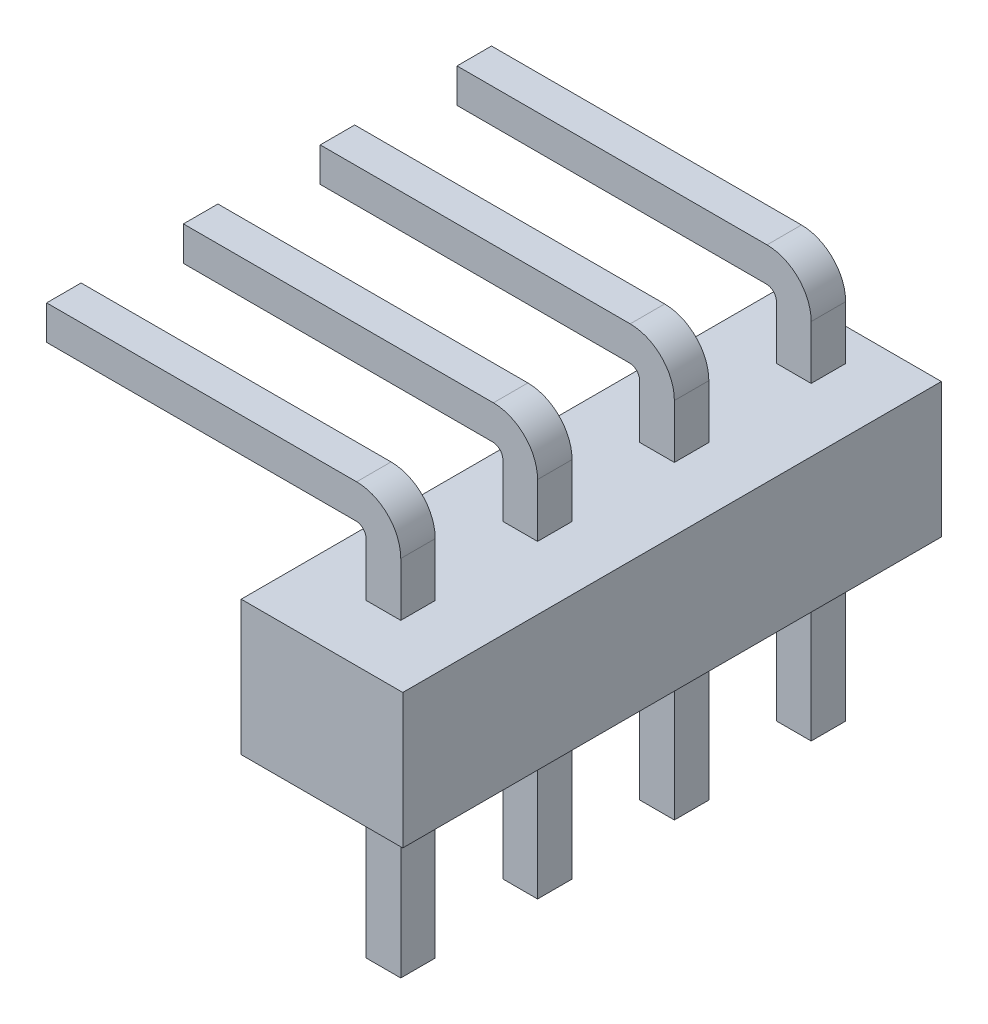
SolidWorks part; units mm, degrees
ref_plane "Front Plane" through (0, 0, 0) normal (0, 0, 1) x (1, 0, 0)
ref_plane "Top Plane" through (0, 0, 0) normal (0, 1, 0) x (1, 0, 0)
ref_plane "Right Plane" through (0, 0, 0) normal (1, 0, 0) x (0, 0, -1)
sketch "Sketch1" plane through (0, 0, 0) normal (0, 0, 1) x (1, 0, 0)
  line L0 (1.5, 0) -> (-1.5, 0) construction
  line L1 (-1.5, 1.25) -> (1.5, 1.25)
  line L2 (-1.5, 1.25) -> (-1.5, -1.25)
  line L3 (-1.5, -1.25) -> (1.5, -1.25)
  line L4 (1.5, 1.25) -> (1.5, -1.25)
  dimension "D1" = 3
  dimension "D2" = 2.5
extrude "Extrude1" add sketch "Sketch1" along normal mid plane 10
ref_plane "Plane4" through (0, 0, 3.86) normal (0, 0, 1) x (1, 0, 0)
sketch "Sketch2" plane through (0, 0, 3.86) normal (0, 0, 1) x (1, 0, 0)
  line L0 (-0.3225, 1.25) -> (-0.3225, 2.245)
  line L1 (1.5, 1.25) -> (-1.5, 1.25) construction
  line L2 (0.3225, 1.25) -> (0.3225, 2.245)
  line L3 (-0.3225, 1.25) -> (0.3225, 1.25)
  line L4 (0, 0) -> (0, 3.2035) construction
  line L5 (-0.5025, 2.4326) -> (-6.5025, 2.4326)
  line L6 (-6.5025, 2.4326) -> (-6.5025, 3.0683)
  line L7 (-6.5025, 3.0683) -> (-0.4975, 3.0683)
  line L8 (-0.3225, -1.25) -> (-0.3225, -4.75)
  line L9 (-1.5, -1.25) -> (1.5, -1.25) construction
  line L10 (-0.3225, -4.75) -> (0.3225, -4.75)
  line L11 (0.3225, -4.75) -> (0.3225, -1.25)
  line L12 (-0.3225, -1.25) -> (0.3225, -1.25)
  arc A0 (-0.3225, 2.245) -> (-0.5025, 2.4326) centre (-0.5103, 2.245) ccw
  arc A1 (0.3225, 2.245) -> (-0.4975, 3.0683) centre (-0.5008, 2.245) ccw
  dimension "D1" = 0.645
  dimension "D2" = 0.995
  dimension "D3" = 0.26
  dimension "D4" = 0.18
  dimension "D5" = 1.162
  dimension "D6" = 0.82
  dimension "D7" = 6
  dimension "D8" = 3.5
extrude "Extrude2" add sketch "Sketch2" against normal blind 0.64
pattern_linear "LPattern1" count 4 spacing 2.54 along (0, 0, -1) of "Extrude2"
chamfer "Chamfer1" distance 0.25 angle 45 32 edges at (-6.5025, 2.4326, 1) (-6.5025, 2.7505, 0.68) (-6.5025, 3.0683, 1) (-6.5025, 2.7505, 1.32) (0.3225, -4.75, 3.54) (0, -4.75, 3.22) (-0.3225, -4.75, 3.54) (0, -4.75, 3.86) (0.3225, -4.75, -1.54) (0, -4.75, -1.86) (-0.3225, -4.75, -1.54) (0, -4.75, -1.22) (0.3225, -4.75, 1) (0, -4.75, 0.68) (-0.3225, -4.75, 1) (0, -4.75, 1.32) (-6.5025, 2.4326, 3.54) (-6.5025, 2.7505, 3.22) (-6.5025, 3.0683, 3.54) (-6.5025, 2.7505, 3.86) (-6.5025, 2.4326, -1.54) (-6.5025, 2.7505, -1.86) (-6.5025, 3.0683, -1.54) (-6.5025, 2.7505, -1.22) (-6.5025, 2.4326, -4.08) (-6.5025, 2.7505, -4.4) (-6.5025, 3.0683, -4.08) (-6.5025, 2.7505, -3.76) (0.3225, -4.75, -4.08) (0, -4.75, -4.4) (-0.3225, -4.75, -4.08) (0, -4.75, -3.76)
